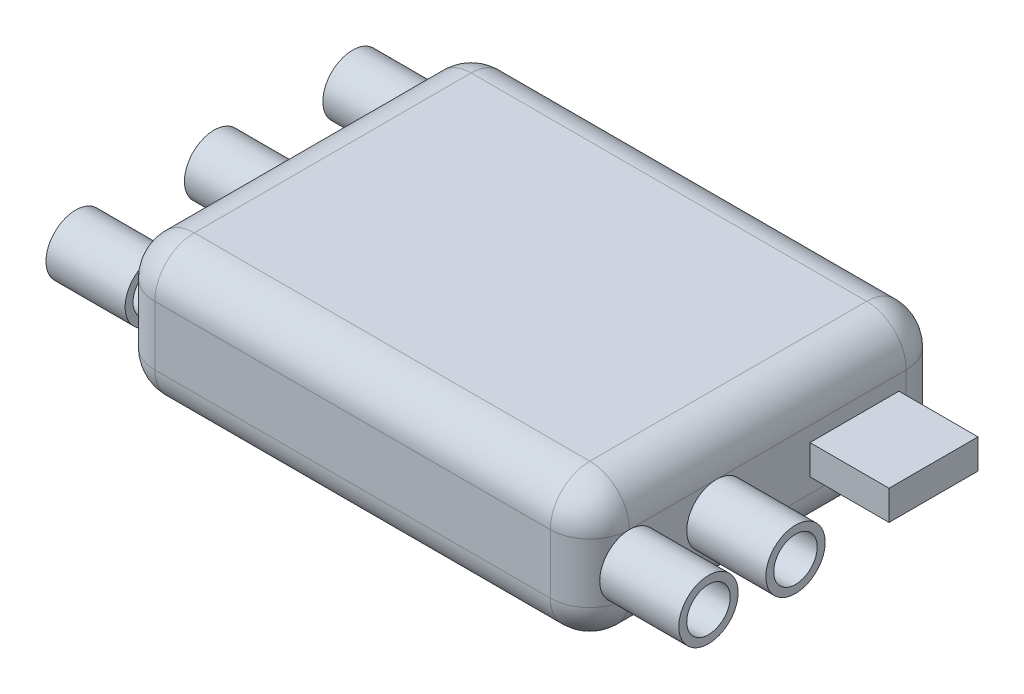
SolidWorks part; units mm, degrees
ref_plane "Front Plane" through (0, 0, 0) normal (0, 0, 1) x (1, 0, 0)
ref_plane "Top Plane" through (0, 0, 0) normal (0, 1, 0) x (1, 0, 0)
ref_plane "Right Plane" through (0, 0, 0) normal (1, 0, 0) x (0, 0, -1)
sketch "Sketch1" plane through (0, 0, 0) normal (0, 1, 0) x (1, 0, 0)
  line L1 (-10, 9) -> (10, 9)
  line L2 (-12, 7) -> (-12, -7)
  line L3 (-10, -9) -> (10, -9)
  line L4 (12, 7) -> (12, -7)
  line L5 (-12, 9) -> (12, -9) construction
  line L6 (-12, -9) -> (12, 9) construction
  arc A0 (10, 9) -> (12, 7) centre (10, 7) cw
  arc A1 (-12, -7) -> (-10, -9) centre (-10, -7) ccw
  arc A2 (-10, 9) -> (-12, 7) centre (-10, 7) ccw
  arc A3 (10, -9) -> (12, -7) centre (10, -7) ccw
  point P0 (0, 0)
  dimension "D3" = 2
  dimension "D1" = 18
  dimension "D2" = 24
extrude "Boss-Extrude1" add sketch "Sketch1" along normal blind 7
fillet "Fillet1" radius 2 16 edges at (0, 0, -9) (-11.4142, 0, -8.4142) (-12, 0, 0) (-11.4142, 0, 8.4142) (0, 0, 9) (11.4142, 0, 8.4142) (12, 0, 0) (11.4142, 0, -8.4142) (12, 7, 0) (11.4142, 7, 8.4142) (0, 7, 9) (-11.4142, 7, 8.4142) (-12, 7, 0) (-11.4142, 7, -8.4142) (0, 7, -9) (11.4142, 7, -8.4142)
sketch "Sketch2" plane through (-12, 0, 0) normal (-1, 0, 0) x (0, 0, 1)
  line L0 (-7, 3.5) -> (7, 3.5) construction
  line L1 (-7, 5) -> (-7, 2) construction
  line L2 (7, 5) -> (7, 2) construction
  circle A0 centre (0, 3.5) radius 1.1
  circle A1 centre (-7, 3.5) radius 1.5
  circle A2 centre (-7, 3.5) radius 1.1
  circle A3 centre (0, 3.5) radius 1.5
  circle A4 centre (7, 3.5) radius 1.1
  circle A5 centre (7, 3.5) radius 1.5
  dimension "D1" = 0.4
extrude "Boss-Extrude2" add sketch "Sketch2" along normal blind 4
sketch "Sketch3" plane through (12, 0, 0) normal (1, 0, 0) x (0, 0, -1)
  line L0 (-7, 3.5) -> (7, 3.5) construction
  line L1 (-7, 5) -> (-7, 2) construction
  line L2 (7, 5) -> (7, 2) construction
  line L4 (2.1292, 4.25) -> (6.6292, 4.25)
  line L5 (2.1292, 4.25) -> (2.1292, 2.75)
  line L6 (2.1292, 2.75) -> (6.6292, 2.75)
  line L7 (6.6292, 4.25) -> (6.6292, 2.75)
  line L8 (2.1292, 4.25) -> (6.6292, 2.75) construction
  line L9 (2.1292, 2.75) -> (6.6292, 4.25) construction
  circle A0 centre (-7, 3.5) radius 1.5
  circle A1 centre (-7, 3.5) radius 1.1
  circle A2 centre (-2.6, 3.5) radius 1.5
  circle A3 centre (-2.6, 3.5) radius 1.1
  point P6 (4.3792, 3.5)
  dimension "D3" = 3
  dimension "D4" = 0.4
  dimension "D1" = 4.5
  dimension "D2" = 1.5
  dimension "D5" = 4.4
extrude "Boss-Extrude3" add sketch "Sketch3" along normal blind 4
